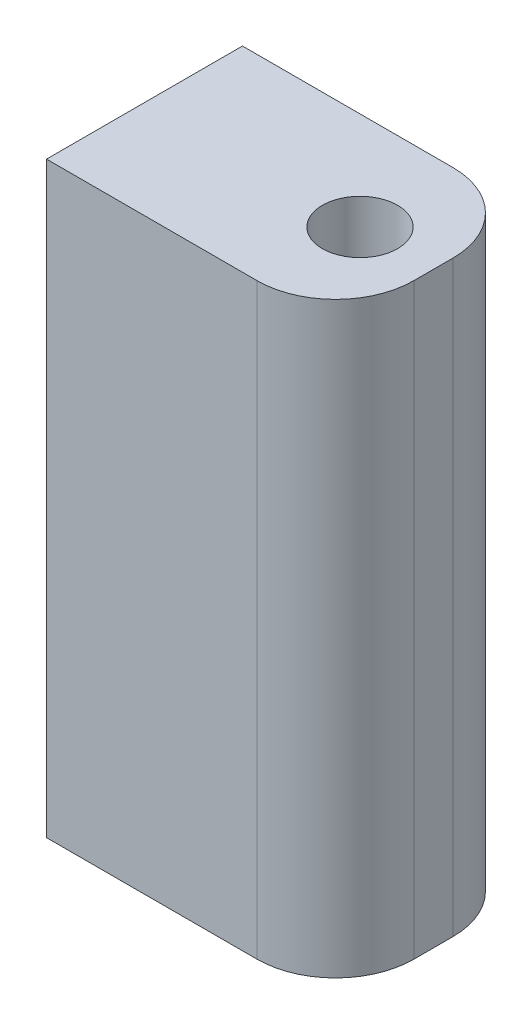
SolidWorks part; units mm, degrees
ref_plane "Front" through (0, 0, 0) normal (0, 0, 1) x (1, 0, 0)
ref_plane "Top" through (0, 0, 0) normal (0, 1, 0) x (1, 0, 0)
ref_plane "Right" through (0, 0, 0) normal (1, 0, 0) x (0, 0, -1)
sketch "Sketch1" plane through (0, 0, 0) normal (0, 0, 1) x (1, 0, 0)
  line L1 (-5, 9.525) -> (5, 9.525)
  line L2 (-5, 9.525) -> (-5, -9.525)
  line L3 (-5, -9.525) -> (5, -9.525)
  line L4 (5, 9.525) -> (5, -9.525)
  line L5 (-5, 9.525) -> (5, -9.525) construction
  line L6 (-5, -9.525) -> (5, 9.525) construction
  point P0 (0, 0)
  dimension "D1" = 10
  dimension "D2" = 19.05
extrude "Boss-Extrude1" add sketch "Sketch1" along normal mid plane 6.35
hole_wizard "#2 Clearance Hole1" positions "Sketch3" profile "Sketch4" hole size "#2" standard "Ansi Inch"
sketch "Sketch3" plane through (0, 9.525, 0) normal (0, 1, 0) x (-1, 0, 0)
  line L0 (-5, 3.175) -> (-5, -3.175) construction
  point P0 (-1.985, 0)
  dimension "D1" = 3.015
sketch "Sketch4" plane through (1.985, 9.525, 0) normal (1, 0, 0) x (0, 0, 1)
  line L0 (0, 0) -> (0, 7.0826)
  line L1 (0, 7.0826) -> (1.2192, 6.35)
  line L2 (1.2192, 6.35) -> (1.2192, 0)
  line L5 (1.2192, 0) -> (0, 0)
  line L10 (0, 7.0826) -> (-1.2192, 6.35) construction
  line L11 (0, -6.35) -> (0, 107.95) construction
  dimension "Hole Dia." = 2.4384
  dimension "Hole Depth" = 6.35
  dimension "Drill Angle" = 118
hole_wizard "#2 Clearance Hole2" positions "Sketch6" profile "Sketch5" hole size "#2" standard "Ansi Inch"
sketch "Sketch6" plane through (-5, 0, 0) normal (-1, 0, 0) x (0, 0, 1)
  line L0 (3.175, -9.525) -> (-3.175, -9.525) construction
  point P0 (0, -2.413)
  dimension "D1" = 7.112
sketch "Sketch5" plane through (-5, -2.413, 0) normal (0, 1, 0) x (0, 0, 1)
  line L0 (0, 0) -> (0, 7.0826)
  line L1 (0, 7.0826) -> (1.2192, 6.35)
  line L2 (1.2192, 6.35) -> (1.2192, 0)
  line L5 (1.2192, 0) -> (0, 0)
  line L10 (0, 7.0826) -> (-1.2192, 6.35) construction
  line L11 (0, -6.35) -> (0, 107.95) construction
  dimension "Hole Dia." = 2.4384
  dimension "Hole Depth" = 6.35
  dimension "Drill Angle" = 118
fillet "Fillet1" radius 1.5875 2 edges at (5, 0, -3.175) (5, 0, 3.175)
sketch "Sketch7" plane through (0, -9.525, 0) normal (0, -1, 0) x (1, 0, 0)
  line L0 (-5, 3.175) -> (3.4125, 3.175) construction
  line L1 (4.365, 3.175) -> (5, 3.175)
  line L2 (4.365, 3.175) -> (4.365, -3.175)
  line L3 (4.365, -3.175) -> (5, -3.175)
  line L4 (5, 3.175) -> (5, -3.175)
  line L5 (-5, -3.175) -> (3.4125, -3.175) construction
  line L6 (5, 1.5875) -> (5, -1.5875) construction
  dimension "D1" = 0.635
extrude "Cut-Extrude1" cut sketch "Sketch7" against normal through all
fillet "Fillet2" radius 2.54 2 edges at (4.365, 0, -2.8575) (4.365, 0, 2.8575)
